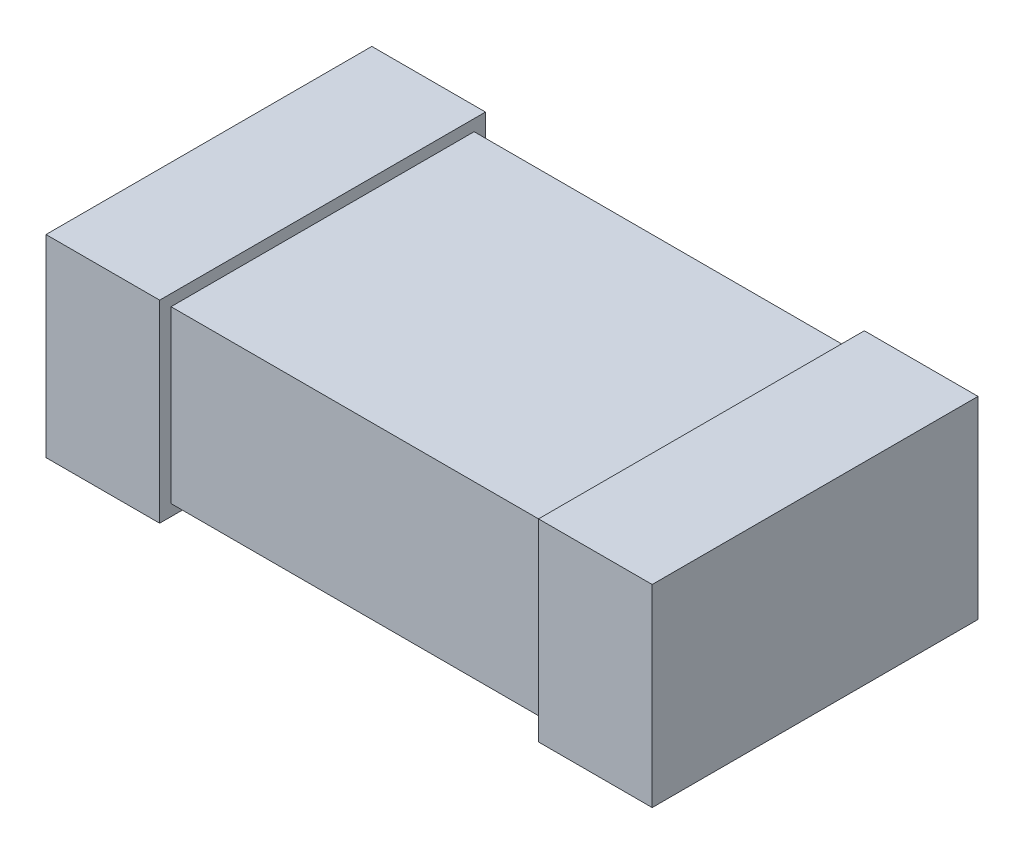
SolidWorks part; units mm, degrees
ref_plane "Front Plane" through (0, 0, 0) normal (0, 0, 1) x (1, 0, 0)
ref_plane "Top Plane" through (0, 0, 0) normal (0, 1, 0) x (1, 0, 0)
ref_plane "Right Plane" through (0, 0, 0) normal (1, 0, 0) x (0, 0, -1)
sketch "Sketch1" plane through (0, 0, 0) normal (0, 1, 0) x (1, 0, 0)
  line L1 (-0.8, 0.4) -> (0.8, 0.4)
  line L2 (-0.8, 0.4) -> (-0.8, -0.4)
  line L3 (-0.8, -0.4) -> (0.8, -0.4)
  line L4 (0.8, 0.4) -> (0.8, -0.4)
  point P4 (0, 0.4)
  point P6 (0.8, 0)
  dimension "D1" = 0.8
  dimension "D2" = 1.6
extrude "Extrude1" add sketch "Sketch1" along normal blind 0.45
sketch "Sketch2" plane through (0, 0, 0) normal (0, 0, 1) x (1, 0, 0)
  line L0 (-0.8, 0.45) -> (-0.8, 0) construction
  line L1 (-0.5, 0.48) -> (-0.8, 0.48)
  line L2 (-0.5, 0.48) -> (-0.5, -0.03)
  line L3 (-0.5, -0.03) -> (-0.8, -0.03)
  line L4 (-0.8, 0.48) -> (-0.8, -0.03)
  line L5 (-0.8, 0.45) -> (0.8, 0.45) construction
  line L6 (-0.8, 0) -> (0.8, 0) construction
  line L7 (0, 0) -> (0, -0.3575) construction
  line L8 (0.8, 0.48) -> (0.8, -0.03)
  line L9 (0.5, -0.03) -> (0.8, -0.03)
  line L10 (0.5, 0.48) -> (0.5, -0.03)
  line L11 (0.5, 0.48) -> (0.8, 0.48)
  dimension "D1" = 0.3
  dimension "D2" = 0.03
  dimension "D3" = 0.03
extrude "Extrude2" add sketch "Sketch2" along normal offset from surface 0.03 and the other way offset from surface (0.43 mm away) 0.03 up to face at (0, 0.225, 0.4) offset beyond the face yes other way up to face at (0, 0.225, -0.4)
ref_plane "Plane1" through (0, -0.03, 0) normal (0, 1, 0) x (-1, 0, 0)
sketch "Component_Outline" plane through (0, -0.03, 0) normal (0, 1, 0) x (-1, 0, 0)
  line L0 (0.8, -0.43) -> (0.5, -0.43)
  line L1 (0.5, -0.43) -> (0.5, -0.4)
  line L2 (0.5, -0.4) -> (-0.5, -0.4)
  line L3 (-0.5, -0.4) -> (-0.5, -0.43)
  line L4 (-0.5, -0.43) -> (-0.8, -0.43)
  line L5 (-0.8, -0.43) -> (-0.8, 0.43)
  line L6 (-0.8, 0.43) -> (-0.5, 0.43)
  line L7 (-0.5, 0.43) -> (-0.5, 0.4)
  line L8 (-0.5, 0.4) -> (0.5, 0.4)
  line L9 (0.5, 0.4) -> (0.5, 0.43)
  line L10 (0.5, 0.43) -> (0.8, 0.43)
  line L11 (0.8, 0.43) -> (0.8, -0.43)
